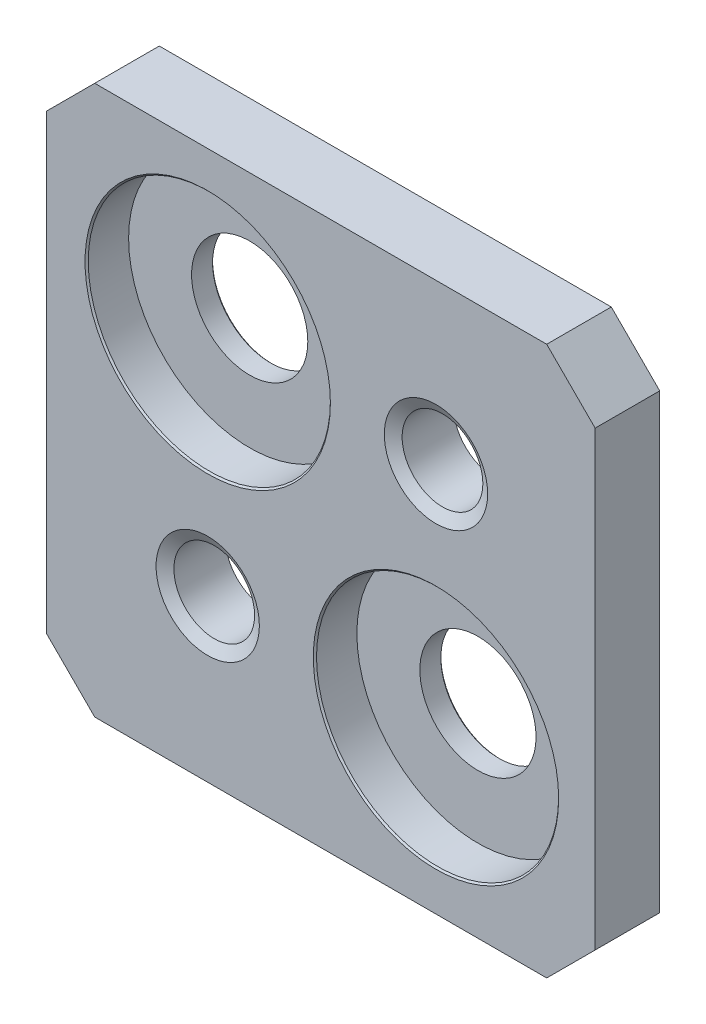
SolidWorks part; units mm, degrees
material "AISI 1045 Сталь, холоднотянутая"
ref_plane "Спереди" through (0, 0, 0) normal (0, 0, 1) x (1, 0, 0)
ref_plane "Сверху" through (0, 0, 0) normal (0, 1, 0) x (1, 0, 0)
ref_plane "Справа" through (0, 0, 0) normal (1, 0, 0) x (0, 0, -1)
sketch "Эскиз1" plane through (0, 0, 0) normal (0, 0, 1) x (1, 0, 0)
  line L0 (0, 15.5) -> (1.5, 17)
  line L1 (1.5, 0) -> (15.5, 0)
  line L2 (0, 1.5) -> (0, 15.5)
  line L3 (1.5, 17) -> (15.5, 17)
  line L4 (17, 1.5) -> (17, 15.5)
  line L5 (15.5, 17) -> (17, 15.5)
  line L6 (15.5, 0) -> (17, 1.5)
  line L7 (0, 1.5) -> (1.5, 0)
  circle A0 centre (5, 5) radius 1
  circle A1 centre (12.07, 5) radius 1
  circle A2 centre (12.07, 12.07) radius 1
  circle A3 centre (5, 12.07) radius 1
  point P0 (0, 0)
  point P1 (17, 17)
  point P2 (0, 17)
  point P3 (17, 0)
  dimension "D3" = 7.07
  dimension "D4" = 7.07
  dimension "D5" = 5
  dimension "D6" = 5
  dimension "D7" = 2
  dimension "D1" = 17
  dimension "D2" = 17
  dimension "D10" = 1.5
  dimension "D11" = 1.5
  dimension "D12" = 1.5
  dimension "D13" = 1.5
extrude "Бобышка-Вытянуть1" add sketch "Эскиз1" along normal blind 2
hole_wizard "Отверстие обработанное метчиком M3x0.51" positions "Эскиз3" profile "Эскиз2" tap size "M3x0.5" standard "Ansi (метрические)" end condition through all
sketch "Эскиз3" plane through (0, 0, 2) normal (0, 0, 1) x (1, 0, 0)
  circle A0 centre (12.07, 12.07) radius 1 construction
  point P0 (12.07, 12.07)
  point P1 (5, 5)
sketch "Эскиз2" plane through (12.07, 12.07, 2) normal (1, 0, 0) x (0, -1, 0)
  line L0 (0, 0) -> (0, 2)
  line L1 (0, 2) -> (1.6, 2)
  line L2 (1.25, 1.7979) -> (1.25, 0.2021)
  line L3 (1.25, 0.2021) -> (1.6, 0)
  line L5 (1.6, 0) -> (0, 0)
  line L6 (-1.25, 0.2021) -> (-1.6, 0) construction
  line L7 (1.6, 2) -> (1.25, 1.7979)
  line L8 (-1.6, 2) -> (-1.25, 1.7979) construction
  line L11 (0, -6.35) -> (0, 107.95) construction
  dimension "Диаметр проходного сверла" = 2.5
  dimension "Глубина проходного сверла" = 2
  dimension "Диаметр передней зенковки" = 3.2
  dimension "Угол передней зенковки" = 120
  dimension "Диаметр задней зенковки" = 3.2
  dimension "Угол задней зенковки" = 120
cosmetic thread "Отверстие резьбы1" parameters "D2"=3
cosmetic thread "Отверстие резьбы2" parameters "D2"=3
hole_wizard "Цековка для винта с заклепочной головкой M31" positions "Эскиз5" profile "Эскиз4" counterbore size "M3" standard "Ansi (метрические)" end condition through all
sketch "Эскиз5" plane through (0, 0, 2) normal (0, 0, 1) x (1, 0, 0)
  circle A0 centre (5, 12.07) radius 1 construction
  point P0 (5, 12.07)
  point P1 (12.07, 5)
sketch "Эскиз4" plane through (5, 12.07, 2) normal (1, 0, 0) x (0, -1, 0)
  line L0 (0, 0) -> (0, 2)
  line L1 (1.8, 1.95) -> (1.85, 2)
  line L2 (3.75, 1.3) -> (1.8, 1.3)
  line L3 (1.8, 1.3) -> (1.8, 1.95)
  line L5 (3.75, 1.3) -> (3.75, 0.05)
  line L6 (3.75, 0.05) -> (3.8, 0)
  line L7 (3.8, 0) -> (0, 0)
  line L8 (-3.75, 0.05) -> (-3.8, 0) construction
  line L11 (0, -6.35) -> (0, 107.95) construction
  line L12 (1.85, 2) -> (0, 2)
  line L13 (-1.8, 1.95) -> (-1.85, 2) construction
  dimension "Диаметр сквозного отверстия" = 3.6
  dimension "Глубина сквозного отверстия" = 2
  dimension "Диаметр цековки" = 7.5
  dimension "Глубина цековки" = 1.3
  dimension "Диаметр передней зенковки" = 7.6
  dimension "Угол передней зенковки" = 90
  dimension "Диаметр задней зенковки" = 3.7
  dimension "Угол задней зенковки" = 90
